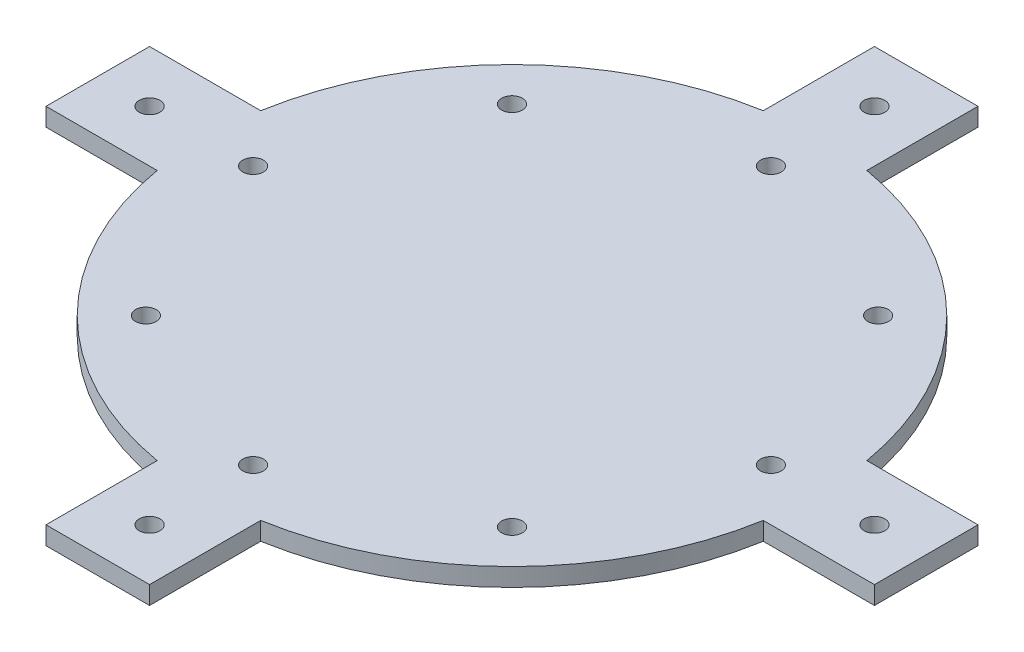
SolidWorks part; units mm, degrees
material "Balsa"
ref_plane "Alzado" through (0, 0, 0) normal (0, 0, 1) x (1, 0, 0)
ref_plane "Planta" through (0, 0, 0) normal (0, 1, 0) x (1, 0, 0)
ref_plane "Vista lateral" through (0, 0, 0) normal (1, 0, 0) x (0, 0, -1)
sketch "Croquis1" plane through (0, 0, 0) normal (0, 1, 0) x (1, 0, 0)
  line L0 (-10, -58.5304) -> (-10, -80)
  line L1 (-10, 80) -> (10, 80)
  line L2 (-10, 80) -> (-10, 58.5304)
  line L3 (-10, -80) -> (10, -80)
  line L4 (10, 80) -> (10, 58.5304)
  line L5 (58.5304, 10) -> (80, 10)
  line L6 (-80, -10) -> (-58.5304, -10)
  line L7 (-80, -10) -> (-80, 10)
  line L8 (-80, 10) -> (-58.5304, 10)
  line L9 (10, -58.5304) -> (10, -80)
  line L10 (80, -10) -> (80, 10)
  line L15 (58.5304, -10) -> (80, -10)
  arc A0 (-10, 58.5304) -> (-58.5304, 10) centre (0, 0) ccw
  circle A1 centre (0, 42) radius 1.8585
  arc A2 (10, -58.5304) -> (58.5304, -10) centre (0, 0) ccw
  arc A3 (-58.5304, -10) -> (-10, -58.5304) centre (0, 0) ccw
  arc A4 (58.5304, 10) -> (10, 58.5304) centre (0, 0) ccw
  dimension "D1" = 42
  dimension "D6" = 80
  dimension "D2" = 160
  dimension "D3" = 20
  dimension "D4" = 20
  dimension "D5" = 160
  dimension "D7" = 80
  dimension "D8" = 10
  dimension "D9" = 10
extrude "Saliente-Extruir1" add sketch "Croquis1" along normal blind 3.5 contours A0 L8 L7 L6 A3 L0 L3 L9 A2 L15 L10 L5 A4 L4 L1 L2
sketch "Croquis2" plane through (0, 3.5, 0) normal (0, 1, 0) x (1, 0, 0)
  circle A0 centre (0, 50) radius 2
  dimension "D1" = 50
  dimension "D2" = 4
extrude "Cortar-Extruir1" cut sketch "Croquis2" against normal up to next (3.5 mm away)
pattern_circular "MatrizC1" count 8 every 45 about axis through (0, 0, 0) along (0, 1, 0) of "Cortar-Extruir1"
sketch "Croquis3" plane through (0, 3.5, 0) normal (0, 1, 0) x (1, 0, 0)
  line L1 (-10, 20) -> (10, 20)
  line L2 (-10, 20) -> (-10, -20)
  line L3 (-10, -20) -> (10, -20)
  line L4 (10, 20) -> (10, -20)
  line L5 (-10, 20) -> (10, -20) construction
  line L6 (-10, -20) -> (10, 20) construction
  point P0 (0, 0)
  dimension "D1" = 40
  dimension "D2" = 20
sketch "Croquis4" plane through (0, 3.5, 0) normal (0, 1, 0) x (1, 0, 0)
  circle A0 centre (0, 70) radius 2
  circle A1 centre (70, 0) radius 2
  circle A2 centre (0, -70) radius 2
  circle A3 centre (-70, 0) radius 2
  point P12 (0, 0)
  dimension "D1" = 70
  dimension "D2" = 4
extrude "Cortar-Extruir2" cut sketch "Croquis4" against normal up to next
